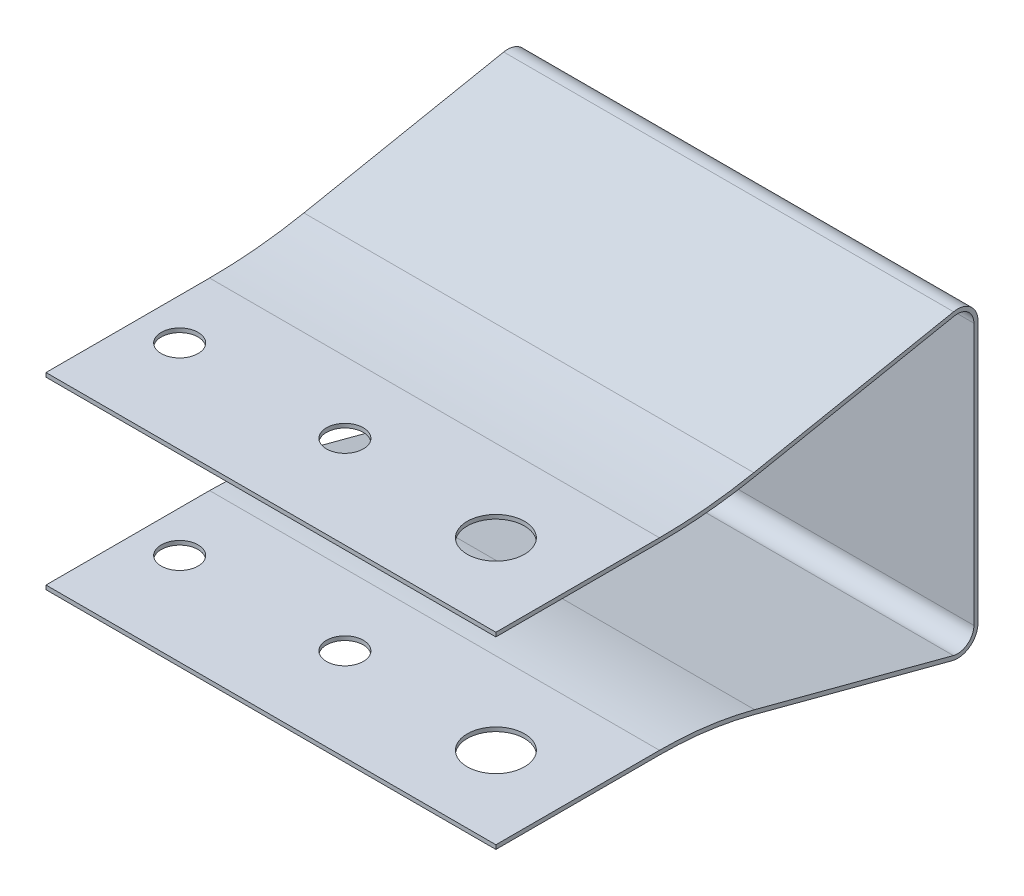
SolidWorks part; units mm, degrees
ref_plane "Front Plane" through (0, 0, 0) normal (0, 0, 1) x (1, 0, 0)
ref_plane "Top Plane" through (0, 0, 0) normal (0, 1, 0) x (1, 0, 0)
ref_plane "Right Plane" through (0, 0, 0) normal (1, 0, 0) x (0, 0, -1)
sketch "Sketch1" plane through (0, 0, 0) normal (1, 0, 0) x (0, 0, -1)
  line L0 (-14.22, 5) -> (-22.22, 5) construction
  line L1 (-24.22, 8) -> (-22.22, 8) construction
  line L2 (-24.22, 8) -> (-24.22, -8) construction
  line L3 (-24.22, -8) -> (-22.22, -8) construction
  line L4 (-14.22, 5) -> (-14.22, 3) construction
  line L5 (-24.22, 8) -> (-14.22, -5) construction
  line L6 (-24.22, -8) -> (-14.22, 5) construction
  line L7 (-22.22, 5) -> (-22.22, 8) construction
  line L8 (-14.22, 3) -> (-21.22, 3) construction
  line L9 (-21.22, 3) -> (-21.22, -3) construction
  line L10 (-21.22, -3) -> (-14.22, -3) construction
  line L11 (-14.22, -5) -> (-22.22, -5) construction
  line L12 (-22.22, -5) -> (-22.22, -8) construction
  line L13 (-14.22, -3) -> (-14.22, -5) construction
  line L14 (-24.22, 8) -> (-24.22, -8)
  line L15 (-10.8136, 6.5687) -> (-23.0262, 8.981)
  line L16 (-5, 5) -> (-5, -5) construction
  line L17 (-5, -5) -> (5, -5) construction
  line L18 (5, 5) -> (5, -5) construction
  line L19 (-5, 5) -> (5, -5) construction
  line L20 (-5, -5) -> (5, 5) construction
  line L21 (-5, 5) -> (5, 5) construction
  line L22 (-5, 5) -> (-5, 6) construction
  line L23 (-5, 6) -> (5, 6) construction
  line L24 (5, 5) -> (5, 6) construction
  line L25 (-10.8136, -5.7553) -> (-22.9645, -8.9668)
  line L26 (-5, -5) -> (5, -5)
  line L27 (-5, 6.25) -> (5, 6.25)
  line L28 (-5, 6) -> (5, 6)
  line L29 (-10.7651, 6.8139) -> (-22.9778, 9.2263)
  line L30 (-24.47, 8) -> (-24.47, -8)
  line L31 (-10.7497, -5.997) -> (-22.9006, -9.2085)
  line L32 (-5, -5.25) -> (5, -5.25)
  line L33 (5, 6.25) -> (5, 6)
  line L34 (5, -5) -> (5, -5.25)
  arc A0 (-24.22, -8) -> (-22.9645, -8.9668) centre (-23.22, -8) ccw
  arc A1 (-23.0262, 8.981) -> (-24.22, 8) centre (-23.22, 8) ccw
  arc A2 (-5, 6.25) -> (-10.7651, 6.8139) centre (-5, 36) cw
  arc A3 (-22.9778, 9.2263) -> (-24.47, 8) centre (-23.22, 8) ccw
  arc A4 (-24.47, -8) -> (-22.9006, -9.2085) centre (-23.22, -8) ccw
  arc A5 (-5, -5.25) -> (-10.7497, -5.997) centre (-5, -27.7512) ccw
  arc A6 (-5, -5) -> (-10.8136, -5.7553) centre (-5, -27.7512) ccw
  arc A7 (-5, 6) -> (-10.8136, 6.5687) centre (-5, 36) cw
  point P0 (-18.0662, 0)
  point P1 (0, 0)
  dimension "D13" = 30
  dimension "D17" = 1
  dimension "D1" = 16
  dimension "D2" = 10
  dimension "D3" = 2
  dimension "D4" = 2
  dimension "D5" = 2
  dimension "D6" = 3
  dimension "D7" = 6
  dimension "D8" = 3
  dimension "D9" = 10
  dimension "D10" = 10
  dimension "D11" = 16.22
  dimension "D12" = 1
  dimension "D14" = 0.25
extrude "Extrude1" add sketch "Sketch1" along normal mid plane 27.5
sketch "Sketch2" plane through (0, 0, 0) normal (0, 1, 0) x (1, 0, 0)
  line L0 (13.75, 5) -> (13.75, -5) construction
  line L1 (13.75, 5) -> (-13.75, 5) construction
  circle A0 centre (8.75, 0) radius 1.75
  circle A1 centre (-1.13, -0.65) radius 1.125
  circle A2 centre (-11.23, -0.65) radius 1.125
  dimension "D1" = 3.5
  dimension "D2" = 2.25
  dimension "D3" = 2.25
  dimension "D4" = 5
  dimension "D5" = 5
  dimension "D6" = 0.65
  dimension "D7" = 14.88
  dimension "D8" = 10.1
extrude "Cut-Extrude1" cut sketch "Sketch2" against normal through all and the other way through all
mirror "Mirror1" about plane through (0, 0, 0) normal (0, 0, 1) of bodies 102
delete or keep bodies "Body-Delete1" type delete bodies bodies 102
